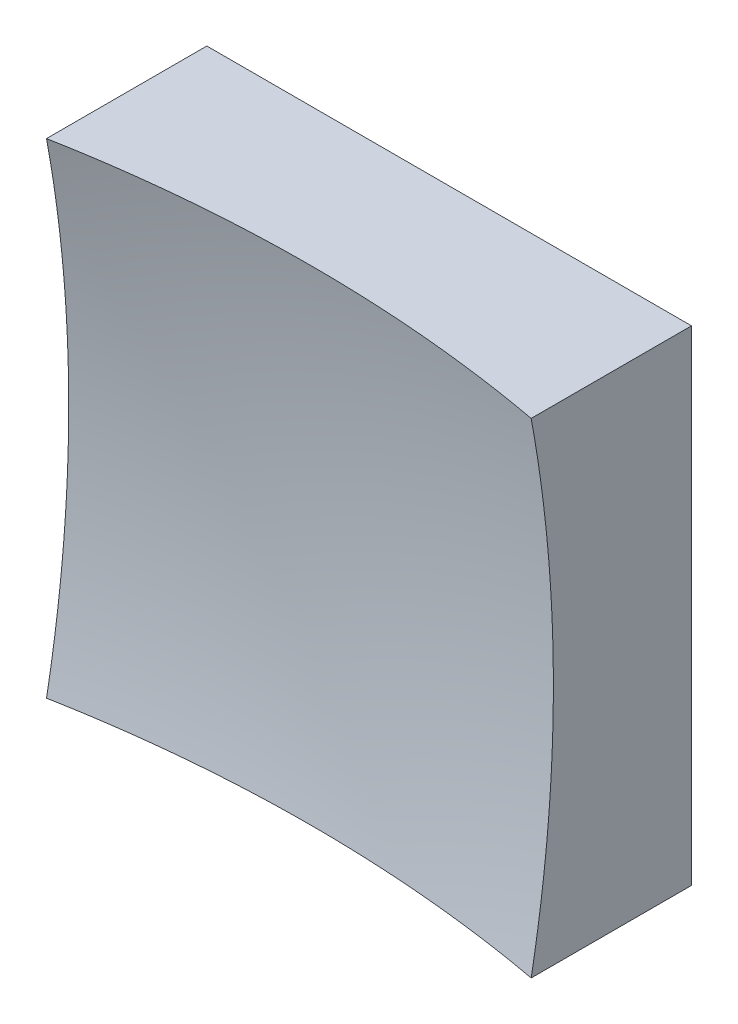
SolidWorks part; units mm, degrees
ref_plane "前视基准面" through (0, 0, 0) normal (0, 0, 1) x (1, 0, 0)
ref_plane "上视基准面" through (0, 0, 0) normal (0, 1, 0) x (1, 0, 0)
ref_plane "右视基准面" through (0, 0, 0) normal (1, 0, 0) x (0, 0, -1)
sketch "草图1" plane through (0, 0, 0) normal (0, 0, 1) x (1, 0, 0)
  line L1 (-12.5, 12.5) -> (12.5, 12.5)
  line L2 (-12.5, 12.5) -> (-12.5, -12.5)
  line L3 (-12.5, -12.5) -> (12.5, -12.5)
  line L4 (12.5, 12.5) -> (12.5, -12.5)
  line L5 (-12.5, 12.5) -> (12.5, -12.5) construction
  line L6 (-12.5, -12.5) -> (12.5, 12.5) construction
  point P0 (0, 0)
  dimension "D1" = 25
  dimension "D2" = 25
extrude "凸台-拉伸1" add sketch "草图1" along normal blind 20 contours L2 L3 L4 L1
sketch "草图2" plane through (0, 0, 0) normal (0, 1, 0) x (1, 0, 0)
  line L0 (-7.4603, -6) -> (7.3192, -6) construction
  line L1 (0, 0) -> (0, -12.1749) construction
  line L2 (68.2392, -60.3983) -> (0, -60.3983)
  line L3 (0, -60.3983) -> (0, -6)
  arc A1 (68.2392, -60.3983) -> (0, -6) centre (0, -76) ccw
  dimension "D2" = 140
  dimension "D1" = 6
revolve "切除-旋转2" cut sketch "草图2" angle 360 about L3
